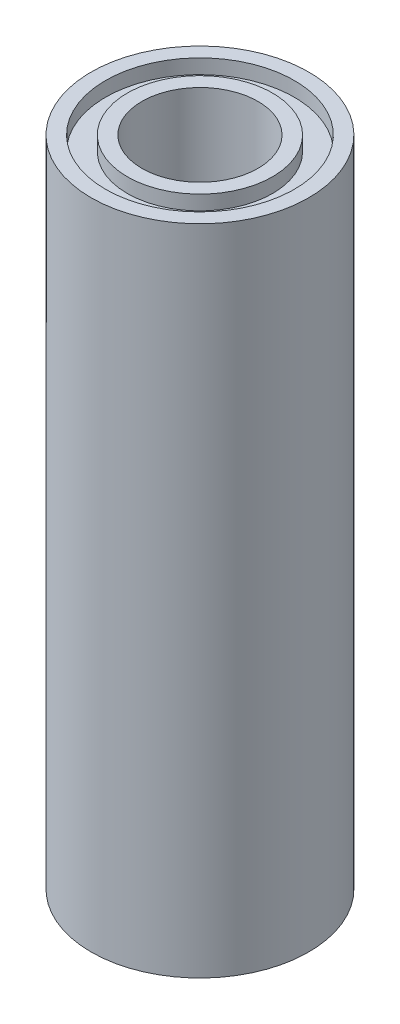
SolidWorks part; units mm, degrees
ref_plane "Front Plane" through (0, 0, 0) normal (0, 0, 1) x (1, 0, 0)
ref_plane "Top Plane" through (0, 0, 0) normal (0, 1, 0) x (1, 0, 0)
ref_plane "Right Plane" through (0, 0, 0) normal (1, 0, 0) x (0, 0, -1)
sketch "Sketch1" plane through (0, 0, 0) normal (0, 1, 0) x (1, 0, 0)
  circle A0 centre (0, 0) radius 7.5
  circle A1 centre (0, 0) radius 4
  point P2 (0, 0)
  dimension "D1" = 8
  dimension "D2" = 15
extrude "Boss-Extrude1" add sketch "Sketch1" along normal blind 45
sketch "Sketch2" plane through (0, 45, 0) normal (0, 1, 0) x (1, 0, 0)
  circle A0 centre (0, 0) radius 6.5
  circle A1 centre (0, 0) radius 5
  circle A2 centre (0, 0) radius 7.5 construction
  dimension "D1" = 10
  dimension "D2" = 13
extrude "Cut-Extrude1" cut sketch "Sketch2" against normal blind 1
